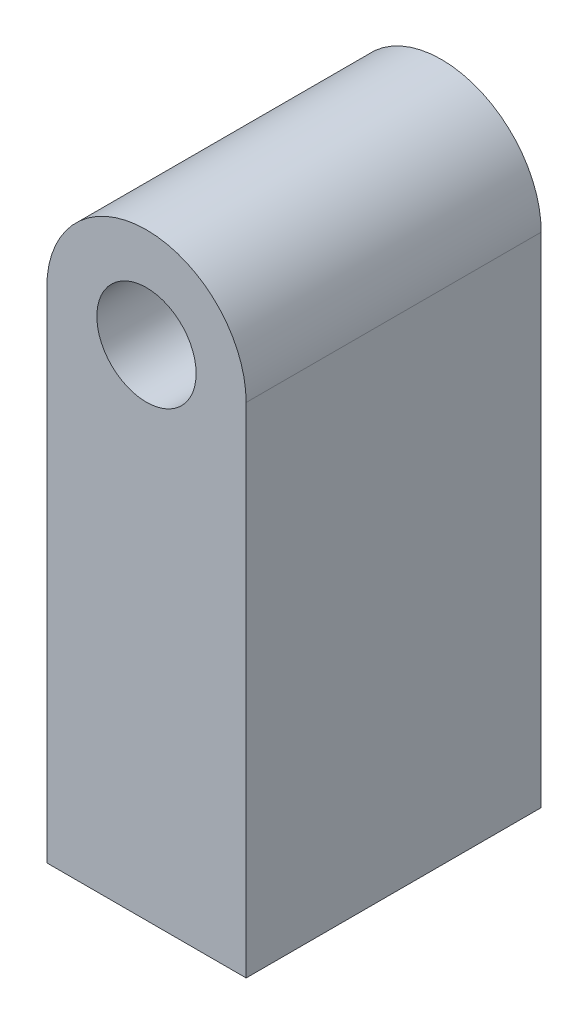
SolidWorks part; units mm, degrees
material "6061-T6 (SS)"
ref_plane "Front Plane" through (0, 0, 0) normal (0, 0, 1) x (1, 0, 0)
ref_plane "Top Plane" through (0, 0, 0) normal (0, 1, 0) x (1, 0, 0)
ref_plane "Right Plane" through (0, 0, 0) normal (1, 0, 0) x (0, 0, -1)
other "Configuration Table"
sketch "Sketch2" plane through (0, 0, 0) normal (0, 0, 1) x (1, 0, 0)
  line L1 (-6.35, 0) -> (6.35, 0)
  line L2 (-6.35, 0) -> (-6.35, 31.75)
  line L3 (-6.35, 31.75) -> (6.35, 31.75) construction
  line L4 (6.35, 0) -> (6.35, 31.75)
  arc A0 (-6.35, 31.75) -> (6.35, 31.75) centre (0, 31.75) cw
  point P4 (0, 0)
  dimension "D1" = 31.75
  dimension "D2" = 12.7
extrude "Boss-Extrude1" add sketch "Sketch2" along normal mid plane 18.796
sketch "Sketch3" plane through (0, 0, 9.398) normal (0, 0, 1) x (1, 0, 0)
  point P0 (0, 31.75)
hole_wizard "1/4 (0.2500) Dowel Hole1" positions "Sketch3" profile "Sketch4" hole size "1/4" standard "ANSI Inch"
sketch "Sketch4" plane through (0, 31.75, 9.398) normal (1, 0, 0) x (0, -1, 0)
  line L0 (0, 0) -> (0, 18.796)
  line L1 (0, 18.796) -> (3.175, 18.796)
  line L2 (3.175, 18.796) -> (3.175, 0)
  line L5 (3.175, 0) -> (0, 0)
  line L11 (0, -6.35) -> (0, 107.95) construction
  dimension "Thru Hole Dia." = 6.35
  dimension "Thru Hole Depth" = 18.796
sketch "Sketch5" plane through (0, 0, 9.398) normal (0, 0, 1) x (1, 0, 0)
  point P0 (0, 31.75)
hole_wizard "1/4 (0.249) Dowel Hole1" positions "Sketch5" profile "Sketch6" hole size "1/4" standard "ANSI Inch" end condition through all
sketch "Sketch6" plane through (0, 31.75, 9.398) normal (1, 0, 0) x (0, -1, 0)
  line L0 (0, 0) -> (0, 18.796)
  line L1 (0, 18.796) -> (3.1623, 18.796)
  line L2 (3.1623, 18.796) -> (3.1623, 0)
  line L5 (3.1623, 0) -> (0, 0)
  line L11 (0, -6.35) -> (0, 107.95) construction
  dimension "Thru Hole Dia." = 6.3246
  dimension "Thru Hole Depth" = 18.796
sketch "Sketch7" plane through (0, 0, 0) normal (0, -1, 0) x (-1, 0, 0)
  point P0 (0, 0)
hole_wizard "1/4-20 Tapped Hole1" positions "Sketch7" profile "Sketch8" tap size "1/4-20" standard "ANSI Inch"
sketch "Sketch8" plane through (0, 0, 0) normal (1, 0, 0) x (0, 0, -1)
  line L0 (0, 0) -> (0, 14.8688)
  line L1 (0, 14.8688) -> (2.5527, 13.335)
  line L2 (2.5527, 13.335) -> (2.5527, 0)
  line L5 (2.5527, 0) -> (0, 0)
  line L10 (0, 14.8688) -> (-2.5527, 13.335) construction
  line L11 (0, -6.35) -> (0, 107.95) construction
  dimension "Tap Drill Dia." = 5.1054
  dimension "Tap Drill Depth" = 13.335
  dimension "Drill Angle" = 118
cosmetic thread "Hole Thread1" parameters "D1"=9.525, "D2"=6.35
